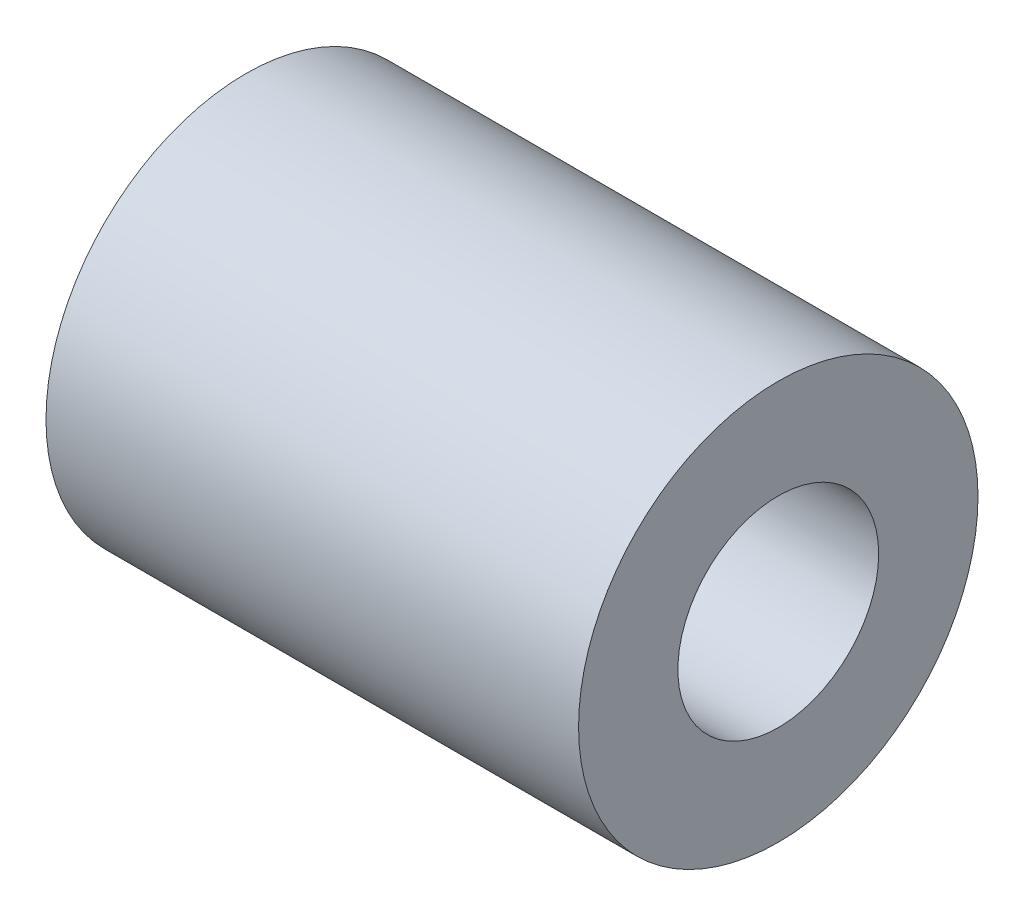
SolidWorks part; units mm, degrees
ref_plane "Front Plane" through (0, 0, 0) normal (0, 0, 1) x (1, 0, 0)
ref_plane "Top Plane" through (0, 0, 0) normal (0, 1, 0) x (1, 0, 0)
ref_plane "Right Plane" through (0, 0, 0) normal (1, 0, 0) x (0, 0, -1)
sketch "Sketch1" plane through (0, 0, 0) normal (1, 0, 0) x (0, 0, -1)
  circle A0 centre (0, 0) radius 4.7879
  circle A1 centre (0, 0) radius 9.525
  dimension "D1" = 9.5758
  dimension "D2" = 19.05
extrude "Boss-Extrude1" add sketch "Sketch1" along normal blind 25.4
